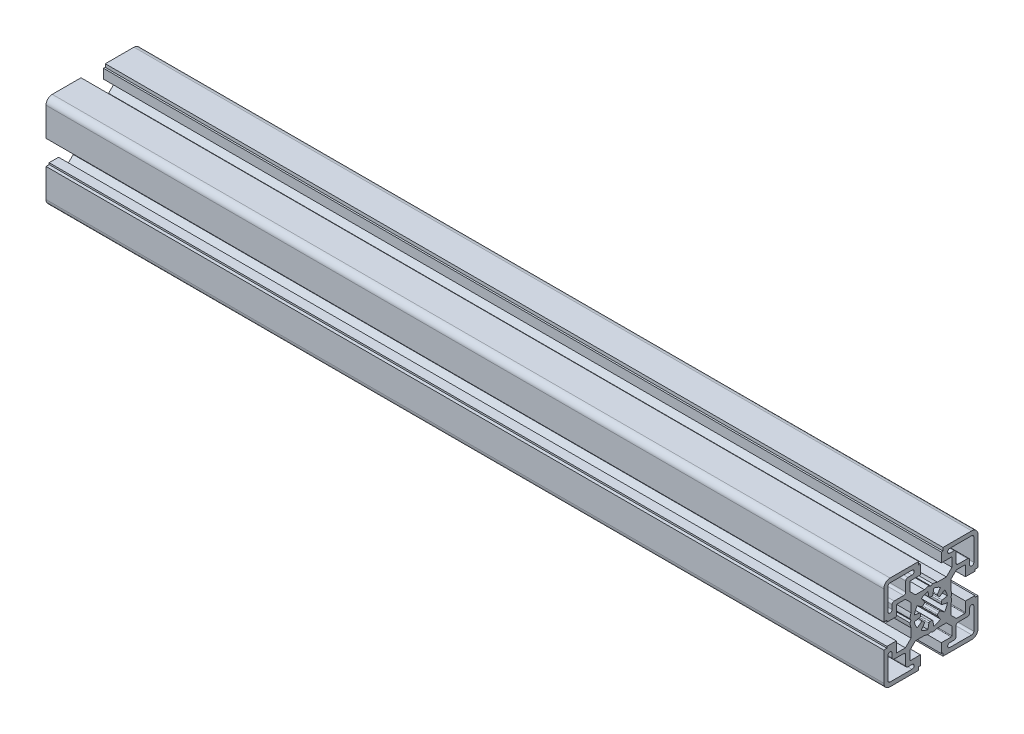
SolidWorks part; units mm, degrees
ref_plane "Спереди" through (0, 0, 0) normal (0, 0, 1) x (1, 0, 0)
ref_plane "Сверху" through (0, 0, 0) normal (0, 1, 0) x (1, 0, 0)
ref_plane "Справа" through (0, 0, 0) normal (1, 0, 0) x (0, 0, -1)
sketch "Эскиз2" plane through (0, 0, 0) normal (1, 0, 0) x (0, 0, -1)
  line L0 (-0.9511, 5.394) -> (-1.3892, 7.8785)
  line L1 (-3.1416, 4.4867) -> (-4.5886, 6.5532)
  line L2 (-4.4867, 3.1416) -> (-6.5532, 4.5886)
  line L3 (7.8785, -1.3892) -> (5.394, -0.9511)
  line L4 (-5.394, 0.9511) -> (-7.8785, 1.3892)
  line L5 (16.5, 5) -> (21, 5)
  line L6 (-21, 5) -> (-16.5, 5)
  line L7 (21, 5.8) -> (22.5, 5.8)
  line L8 (-22.5, 5.8) -> (-21, 5.8)
  line L9 (3.1225, 9.5) -> (7.3787, 9.5)
  line L10 (-7.3787, 9.5) -> (-3.1225, 9.5)
  line L11 (12.1713, 10.05) -> (16.2, 10.05)
  line L12 (-16.2, 10.05) -> (-12.1713, 10.05)
  line L13 (-17.5, 12) -> (-13, 12)
  line L14 (5, 16.5) -> (9.75, 16.5)
  line L15 (-9.75, 16.5) -> (-5, 16.5)
  line L16 (-19.5, 20.5) -> (-9, 20.5)
  line L17 (5, 21) -> (5.8, 21)
  line L18 (-5.8, 21) -> (-5, 21)
  line L19 (5.8, 22.5) -> (19.5, 22.5)
  line L20 (-19.5, 22.5) -> (-5.8, 22.5)
  line L21 (-7.8785, -1.3892) -> (-5.394, -0.9511)
  line L22 (5.394, 0.9511) -> (7.8785, 1.3892)
  line L23 (4.4867, 3.1416) -> (6.5532, 4.5886)
  line L24 (3.1416, 4.4867) -> (4.5886, 6.5532)
  line L25 (0.9511, 5.394) -> (1.3892, 7.8785)
  line L26 (-22.5, 5.8) -> (-22.5, 19.5)
  line L27 (-21, 5) -> (-21, 5.8)
  line L28 (-20.5, 9) -> (-20.5, 19.5)
  line L29 (-16.5, 5) -> (-16.5, 9.75)
  line L30 (-12, 13) -> (-12, 17.5)
  line L31 (-5.8, 21) -> (-5.8, 22.5)
  line L32 (-5, 16.5) -> (-5, 21)
  line L33 (5, 16.5) -> (5, 21)
  line L34 (5.8, 21) -> (5.8, 22.5)
  line L35 (9.5, 3.1225) -> (9.5, 7.3787)
  line L36 (10.05, 12.1713) -> (10.05, 16.2)
  line L37 (16.5, 5) -> (16.5, 9.75)
  line L38 (21, 5) -> (21, 5.8)
  line L39 (22.5, 5.8) -> (22.5, 19.5)
  line L40 (1.3892, -7.8785) -> (0.9511, -5.394)
  line L41 (4.5886, -6.5532) -> (3.1416, -4.4867)
  line L42 (6.5532, -4.5886) -> (4.4867, -3.1416)
  line L43 (-7.3787, -9.5) -> (-3.1225, -9.5)
  line L44 (3.1225, -9.5) -> (7.3787, -9.5)
  line L45 (-6.5532, -4.5886) -> (-4.4867, -3.1416)
  line L46 (-4.5886, -6.5532) -> (-3.1416, -4.4867)
  line L47 (-1.3892, -7.8785) -> (-0.9511, -5.394)
  line L48 (-9.5, -7.3787) -> (-9.5, -3.1225)
  line L49 (9.5, -7.3787) -> (9.5, -3.1225)
  line L50 (-22.5, -5.8) -> (-21, -5.8)
  line L51 (-21, -5) -> (-16.5, -5)
  line L52 (-21, -5.8) -> (-21, -5)
  line L53 (-16.5, -9.75) -> (-16.5, -5)
  line L54 (-22.5, -19.5) -> (-22.5, -5.8)
  line L55 (21, -5.8) -> (22.5, -5.8)
  line L56 (16.5, -5) -> (21, -5)
  line L57 (21, -5.8) -> (21, -5)
  line L58 (16.5, -9.75) -> (16.5, -5)
  line L59 (12.1713, -10.05) -> (16.2, -10.05)
  line L60 (22.5, -19.5) -> (22.5, -5.8)
  line L61 (-16.2, -10.05) -> (-12.1713, -10.05)
  line L62 (5, -16.5) -> (9.75, -16.5)
  line L63 (-9.75, -16.5) -> (-5, -16.5)
  line L64 (5, -21) -> (5.8, -21)
  line L65 (-5.8, -21) -> (-5, -21)
  line L66 (5.8, -22.5) -> (19.5, -22.5)
  line L67 (-19.5, -22.5) -> (-5.8, -22.5)
  line L68 (-10.05, -12.1713) -> (-10.05, -16.2)
  line L69 (-5.8, -21) -> (-5.8, -22.5)
  line L70 (-5, -16.5) -> (-5, -21)
  line L71 (5, -16.5) -> (5, -21)
  line L72 (5.8, -21) -> (5.8, -22.5)
  line L73 (10.05, -12.1713) -> (10.05, -16.2)
  line L74 (-9.5, 3.1225) -> (-9.5, 7.3787)
  line L75 (-9.5, 7.3787) -> (-12.1713, 10.05)
  line L76 (7.3787, 9.5) -> (10.05, 12.1713)
  line L77 (9.5, 7.3787) -> (12.1713, 10.05)
  line L78 (9.5, -7.3787) -> (12.1713, -10.05)
  line L79 (7.3787, -9.5) -> (10.05, -12.1713)
  line L80 (-7.3787, -9.5) -> (-10.05, -12.1713)
  line L81 (-12.1713, -10.05) -> (-9.5, -7.3787)
  line L82 (-10.05, 12.1713) -> (-10.05, 16.2)
  line L83 (-10.05, 12.1713) -> (-7.3787, 9.5)
  line L84 (-9.4624, 0) -> (-9.9624, 0.866)
  line L85 (-9.4624, 0) -> (-9.9624, -0.866)
  line L86 (0, -9.4624) -> (-0.866, -9.9624)
  line L87 (0, -9.4624) -> (0.866, -9.9624)
  line L88 (0, 9.4624) -> (0.866, 9.9624)
  line L89 (0, 9.4624) -> (-0.866, 9.9624)
  line L90 (9.4624, 0) -> (9.9624, -0.866)
  line L91 (9.4624, 0) -> (9.9624, 0.866)
  line L92 (-11, 18.5) -> (-9, 18.5)
  line L93 (-18.5, 11) -> (-18.5, 9)
  line L94 (17.5, 12) -> (13, 12)
  line L95 (12, 13) -> (12, 17.5)
  line L96 (19.5, 20.5) -> (9, 20.5)
  line L97 (11, 18.5) -> (9, 18.5)
  line L98 (20.5, 9) -> (20.5, 19.5)
  line L99 (18.5, 11) -> (18.5, 9)
  line L100 (-17.5, -12) -> (-13, -12)
  line L101 (-12, -13) -> (-12, -17.5)
  line L102 (-19.5, -20.5) -> (-9, -20.5)
  line L103 (-11, -18.5) -> (-9, -18.5)
  line L104 (-20.5, -9) -> (-20.5, -19.5)
  line L105 (-18.5, -11) -> (-18.5, -9)
  line L106 (19.5, -20.5) -> (9, -20.5)
  line L107 (11, -18.5) -> (9, -18.5)
  line L108 (17.5, -12) -> (13, -12)
  line L109 (12, -13) -> (12, -17.5)
  line L110 (20.5, -9) -> (20.5, -19.5)
  line L111 (18.5, -11) -> (18.5, -9)
  arc A0 (-19.5, 20.5) -> (-20.5, 19.5) centre (-19.5, 19.5) ccw
  arc A1 (-19.5, 22.5) -> (-22.5, 19.5) centre (-19.5, 19.5) ccw
  arc A2 (-13, 12) -> (-12, 13) centre (-13, 13) ccw
  arc A3 (-3.2283, 3.8181) -> (-3.8181, 3.2283) centre (0, 0) ccw
  arc A4 (3.8181, 3.2283) -> (3.2283, 3.8181) centre (0, 0) ccw
  arc A5 (-4.9826, 0.417) -> (-4.9826, -0.417) centre (0, 0) ccw
  arc A6 (0.417, 4.9826) -> (-0.417, 4.9826) centre (0, 0) ccw
  arc A7 (4.9826, -0.417) -> (4.9826, 0.417) centre (0, 0) ccw
  arc A8 (-6.5532, 4.5886) -> (-7.8785, 1.3892) centre (0, 0) ccw
  arc A9 (-1.3892, 7.8785) -> (-4.5886, 6.5532) centre (0, 0) ccw
  arc A10 (4.5886, 6.5532) -> (1.3892, 7.8785) centre (0, 0) ccw
  arc A11 (7.8785, 1.3892) -> (6.5532, 4.5886) centre (0, 0) ccw
  arc A12 (22.5, 19.5) -> (19.5, 22.5) centre (19.5, 19.5) ccw
  arc A13 (3.2283, -3.8181) -> (3.8181, -3.2283) centre (0, 0) ccw
  arc A14 (-3.8181, -3.2283) -> (-3.2283, -3.8181) centre (0, 0) ccw
  arc A15 (-0.417, -4.9826) -> (0.417, -4.9826) centre (0, 0) ccw
  arc A16 (6.5532, -4.5886) -> (7.8785, -1.3892) centre (0, 0) ccw
  arc A17 (1.3892, -7.8785) -> (4.5886, -6.5532) centre (0, 0) ccw
  arc A18 (-4.5886, -6.5532) -> (-1.3892, -7.8785) centre (0, 0) ccw
  arc A19 (-7.8785, -1.3892) -> (-6.5532, -4.5886) centre (0, 0) ccw
  arc A20 (-22.5, -19.5) -> (-19.5, -22.5) centre (-19.5, -19.5) ccw
  arc A21 (19.5, -22.5) -> (22.5, -19.5) centre (19.5, -19.5) ccw
  arc A22 (-4.4867, 3.1416) -> (-3.8181, 3.2283) centre (-4.1999, 3.5512) ccw
  arc A23 (-3.2283, 3.8181) -> (-3.1416, 4.4867) centre (-3.5512, 4.1999) ccw
  arc A24 (-0.9511, 5.394) -> (-0.417, 4.9826) centre (-0.4587, 5.4808) ccw
  arc A25 (0.417, 4.9826) -> (0.9511, 5.394) centre (0.4587, 5.4808) ccw
  arc A26 (3.1416, 4.4867) -> (3.2283, 3.8181) centre (3.5512, 4.1999) ccw
  arc A27 (3.8181, 3.2283) -> (4.4867, 3.1416) centre (4.1999, 3.5512) ccw
  arc A28 (5.394, 0.9511) -> (4.9826, 0.417) centre (5.4808, 0.4587) ccw
  arc A29 (4.9826, -0.417) -> (5.394, -0.9511) centre (5.4808, -0.4587) ccw
  arc A30 (4.4867, -3.1416) -> (3.8181, -3.2283) centre (4.1999, -3.5512) ccw
  arc A31 (3.2283, -3.8181) -> (3.1416, -4.4867) centre (3.5512, -4.1999) ccw
  arc A32 (0.9511, -5.394) -> (0.417, -4.9826) centre (0.4587, -5.4808) ccw
  arc A33 (-0.417, -4.9826) -> (-0.9511, -5.394) centre (-0.4587, -5.4808) ccw
  arc A34 (-3.1416, -4.4867) -> (-3.2283, -3.8181) centre (-3.5512, -4.1999) ccw
  arc A35 (-3.8181, -3.2283) -> (-4.4867, -3.1416) centre (-4.1999, -3.5512) ccw
  arc A36 (-5.394, -0.9511) -> (-4.9826, -0.417) centre (-5.4808, -0.4587) ccw
  arc A37 (-4.9826, 0.417) -> (-5.394, 0.9511) centre (-5.4808, 0.4587) ccw
  arc A38 (-16.5, -9.75) -> (-16.2, -10.05) centre (-16.2, -9.75) ccw
  arc A39 (-10.05, -16.2) -> (-9.75, -16.5) centre (-9.75, -16.2) ccw
  arc A40 (9.75, -16.5) -> (10.05, -16.2) centre (9.75, -16.2) ccw
  arc A41 (16.2, -10.05) -> (16.5, -9.75) centre (16.2, -9.75) ccw
  arc A42 (16.5, 9.75) -> (16.2, 10.05) centre (16.2, 9.75) ccw
  arc A43 (10.05, 16.2) -> (9.75, 16.5) centre (9.75, 16.2) ccw
  arc A44 (-9.75, 16.5) -> (-10.05, 16.2) centre (-9.75, 16.2) ccw
  arc A45 (-16.2, 10.05) -> (-16.5, 9.75) centre (-16.2, 9.75) ccw
  arc A46 (-9.9624, -0.866) -> (-9.5, -3.1225) centre (0, 0) ccw
  arc A47 (-9.5, 3.1225) -> (-9.9624, 0.866) centre (0, 0) ccw
  arc A48 (-3.1225, -9.5) -> (-0.866, -9.9624) centre (0, 0) ccw
  arc A49 (3.1225, 9.5) -> (0.866, 9.9624) centre (0, 0) ccw
  arc A50 (9.5, -3.1225) -> (9.9624, -0.866) centre (0, 0) ccw
  arc A51 (-0.866, 9.9624) -> (-3.1225, 9.5) centre (0, 0) ccw
  arc A52 (9.9624, 0.866) -> (9.5, 3.1225) centre (0, 0) ccw
  arc A53 (0.866, -9.9624) -> (3.1225, -9.5) centre (0, 0) ccw
  arc A54 (-11, 18.5) -> (-12, 17.5) centre (-11, 17.5) ccw
  arc A55 (-9, 18.5) -> (-9, 20.5) centre (-9, 19.5) ccw
  arc A56 (-17.5, 12) -> (-18.5, 11) centre (-17.5, 11) ccw
  arc A57 (-20.5, 9) -> (-18.5, 9) centre (-19.5, 9) ccw
  arc A58 (20.5, 19.5) -> (19.5, 20.5) centre (19.5, 19.5) ccw
  arc A59 (12, 13) -> (13, 12) centre (13, 13) ccw
  arc A60 (12, 17.5) -> (11, 18.5) centre (11, 17.5) ccw
  arc A61 (18.5, 11) -> (17.5, 12) centre (17.5, 11) ccw
  arc A62 (9, 20.5) -> (9, 18.5) centre (9, 19.5) ccw
  arc A63 (18.5, 9) -> (20.5, 9) centre (19.5, 9) ccw
  arc A64 (-20.5, -19.5) -> (-19.5, -20.5) centre (-19.5, -19.5) ccw
  arc A65 (-12, -13) -> (-13, -12) centre (-13, -13) ccw
  arc A66 (-12, -17.5) -> (-11, -18.5) centre (-11, -17.5) ccw
  arc A67 (-18.5, -11) -> (-17.5, -12) centre (-17.5, -11) ccw
  arc A68 (-9, -20.5) -> (-9, -18.5) centre (-9, -19.5) ccw
  arc A69 (-18.5, -9) -> (-20.5, -9) centre (-19.5, -9) ccw
  arc A70 (19.5, -20.5) -> (20.5, -19.5) centre (19.5, -19.5) ccw
  arc A71 (11, -18.5) -> (12, -17.5) centre (11, -17.5) ccw
  arc A72 (9, -18.5) -> (9, -20.5) centre (9, -19.5) ccw
  arc A73 (13, -12) -> (12, -13) centre (13, -13) ccw
  arc A74 (17.5, -12) -> (18.5, -11) centre (17.5, -11) ccw
  arc A75 (20.5, -9) -> (18.5, -9) centre (19.5, -9) ccw
extrude "Бобышка-Вытянуть1" add sketch "Эскиз2" along normal blind 400 contours L75 L12 A45 L29 L6 L27 L8 L26 A1 L20 L31 L18 L32 L15 A44 L82 L83 L10 A51 L89 L88 A49 L9 L76 L36 A43 L14 L33 L17 L34 L19 A12 L39 L7 L38 L5 L37 A42 L11 L77 L35 A52 L91 L90 A50 L49 L78 L59 A41 L58 L56 L57 L55 L60 A21 L66 L72 L64 L71 L62 A40 L73 L79 L44 A53 L87 L86 A48 L43 L80 L68 A39 L63 L70 L65 L69 L67 A20 L54 L50 L52 L51 L53 A38 L61 L81 L48 A46 L85 L84 A47 L74
sketch "Эскиз3" plane through (0, 0, 0) normal (-1, 0, 0) x (0, 0, 1)
  line L0 (-0.9511, 5.394) -> (-1.3892, 7.8785)
  line L1 (-3.1416, 4.4867) -> (-4.5886, 6.5532)
  line L2 (-4.4867, 3.1416) -> (-6.5532, 4.5886)
  line L3 (7.8785, -1.3892) -> (5.394, -0.9511)
  line L4 (-5.394, 0.9511) -> (-7.8785, 1.3892)
  line L13 (-17.5, 12) -> (-13, 12)
  line L16 (-19.5, 20.5) -> (-9, 20.5)
  line L21 (-7.8785, -1.3892) -> (-5.394, -0.9511)
  line L22 (5.394, 0.9511) -> (7.8785, 1.3892)
  line L23 (4.4867, 3.1416) -> (6.5532, 4.5886)
  line L24 (3.1416, 4.4867) -> (4.5886, 6.5532)
  line L25 (0.9511, 5.394) -> (1.3892, 7.8785)
  line L28 (-20.5, 9) -> (-20.5, 19.5)
  line L30 (-12, 13) -> (-12, 17.5)
  line L40 (1.3892, -7.8785) -> (0.9511, -5.394)
  line L41 (4.5886, -6.5532) -> (3.1416, -4.4867)
  line L42 (6.5532, -4.5886) -> (4.4867, -3.1416)
  line L45 (-6.5532, -4.5886) -> (-4.4867, -3.1416)
  line L46 (-4.5886, -6.5532) -> (-3.1416, -4.4867)
  line L47 (-1.3892, -7.8785) -> (-0.9511, -5.394)
  line L92 (-11, 18.5) -> (-9, 18.5)
  line L93 (-18.5, 11) -> (-18.5, 9)
  line L94 (17.5, 12) -> (13, 12)
  line L95 (12, 13) -> (12, 17.5)
  line L96 (19.5, 20.5) -> (9, 20.5)
  line L97 (11, 18.5) -> (9, 18.5)
  line L98 (20.5, 9) -> (20.5, 19.5)
  line L99 (18.5, 11) -> (18.5, 9)
  line L100 (-17.5, -12) -> (-13, -12)
  line L101 (-12, -13) -> (-12, -17.5)
  line L102 (-19.5, -20.5) -> (-9, -20.5)
  line L103 (-11, -18.5) -> (-9, -18.5)
  line L104 (-20.5, -9) -> (-20.5, -19.5)
  line L105 (-18.5, -11) -> (-18.5, -9)
  line L106 (19.5, -20.5) -> (9, -20.5)
  line L107 (11, -18.5) -> (9, -18.5)
  line L108 (17.5, -12) -> (13, -12)
  line L109 (12, -13) -> (12, -17.5)
  line L110 (20.5, -9) -> (20.5, -19.5)
  line L111 (18.5, -11) -> (18.5, -9)
  arc A0 (-19.5, 20.5) -> (-20.5, 19.5) centre (-19.5, 19.5) ccw
  arc A2 (-13, 12) -> (-12, 13) centre (-13, 13) ccw
  arc A3 (-3.2283, 3.8181) -> (-3.8181, 3.2283) centre (0, 0) ccw
  arc A4 (3.8181, 3.2283) -> (3.2283, 3.8181) centre (0, 0) ccw
  arc A5 (-4.9826, 0.417) -> (-4.9826, -0.417) centre (0, 0) ccw
  arc A6 (0.417, 4.9826) -> (-0.417, 4.9826) centre (0, 0) ccw
  arc A7 (4.9826, -0.417) -> (4.9826, 0.417) centre (0, 0) ccw
  arc A8 (-6.5532, 4.5886) -> (-7.8785, 1.3892) centre (0, 0) ccw
  arc A9 (-1.3892, 7.8785) -> (-4.5886, 6.5532) centre (0, 0) ccw
  arc A10 (4.5886, 6.5532) -> (1.3892, 7.8785) centre (0, 0) ccw
  arc A11 (7.8785, 1.3892) -> (6.5532, 4.5886) centre (0, 0) ccw
  arc A13 (3.2283, -3.8181) -> (3.8181, -3.2283) centre (0, 0) ccw
  arc A14 (-3.8181, -3.2283) -> (-3.2283, -3.8181) centre (0, 0) ccw
  arc A15 (-0.417, -4.9826) -> (0.417, -4.9826) centre (0, 0) ccw
  arc A16 (6.5532, -4.5886) -> (7.8785, -1.3892) centre (0, 0) ccw
  arc A17 (1.3892, -7.8785) -> (4.5886, -6.5532) centre (0, 0) ccw
  arc A18 (-4.5886, -6.5532) -> (-1.3892, -7.8785) centre (0, 0) ccw
  arc A19 (-7.8785, -1.3892) -> (-6.5532, -4.5886) centre (0, 0) ccw
  arc A22 (-4.4867, 3.1416) -> (-3.8181, 3.2283) centre (-4.1999, 3.5512) ccw
  arc A23 (-3.2283, 3.8181) -> (-3.1416, 4.4867) centre (-3.5512, 4.1999) ccw
  arc A24 (-0.9511, 5.394) -> (-0.417, 4.9826) centre (-0.4587, 5.4808) ccw
  arc A25 (0.417, 4.9826) -> (0.9511, 5.394) centre (0.4587, 5.4808) ccw
  arc A26 (3.1416, 4.4867) -> (3.2283, 3.8181) centre (3.5512, 4.1999) ccw
  arc A27 (3.8181, 3.2283) -> (4.4867, 3.1416) centre (4.1999, 3.5512) ccw
  arc A28 (5.394, 0.9511) -> (4.9826, 0.417) centre (5.4808, 0.4587) ccw
  arc A29 (4.9826, -0.417) -> (5.394, -0.9511) centre (5.4808, -0.4587) ccw
  arc A30 (4.4867, -3.1416) -> (3.8181, -3.2283) centre (4.1999, -3.5512) ccw
  arc A31 (3.2283, -3.8181) -> (3.1416, -4.4867) centre (3.5512, -4.1999) ccw
  arc A32 (0.9511, -5.394) -> (0.417, -4.9826) centre (0.4587, -5.4808) ccw
  arc A33 (-0.417, -4.9826) -> (-0.9511, -5.394) centre (-0.4587, -5.4808) ccw
  arc A34 (-3.1416, -4.4867) -> (-3.2283, -3.8181) centre (-3.5512, -4.1999) ccw
  arc A35 (-3.8181, -3.2283) -> (-4.4867, -3.1416) centre (-4.1999, -3.5512) ccw
  arc A36 (-5.394, -0.9511) -> (-4.9826, -0.417) centre (-5.4808, -0.4587) ccw
  arc A37 (-4.9826, 0.417) -> (-5.394, 0.9511) centre (-5.4808, 0.4587) ccw
  arc A54 (-11, 18.5) -> (-12, 17.5) centre (-11, 17.5) ccw
  arc A55 (-9, 18.5) -> (-9, 20.5) centre (-9, 19.5) ccw
  arc A56 (-17.5, 12) -> (-18.5, 11) centre (-17.5, 11) ccw
  arc A57 (-20.5, 9) -> (-18.5, 9) centre (-19.5, 9) ccw
  arc A58 (20.5, 19.5) -> (19.5, 20.5) centre (19.5, 19.5) ccw
  arc A59 (12, 13) -> (13, 12) centre (13, 13) ccw
  arc A60 (12, 17.5) -> (11, 18.5) centre (11, 17.5) ccw
  arc A61 (18.5, 11) -> (17.5, 12) centre (17.5, 11) ccw
  arc A62 (9, 20.5) -> (9, 18.5) centre (9, 19.5) ccw
  arc A63 (18.5, 9) -> (20.5, 9) centre (19.5, 9) ccw
  arc A64 (-20.5, -19.5) -> (-19.5, -20.5) centre (-19.5, -19.5) ccw
  arc A65 (-12, -13) -> (-13, -12) centre (-13, -13) ccw
  arc A66 (-12, -17.5) -> (-11, -18.5) centre (-11, -17.5) ccw
  arc A67 (-18.5, -11) -> (-17.5, -12) centre (-17.5, -11) ccw
  arc A68 (-9, -20.5) -> (-9, -18.5) centre (-9, -19.5) ccw
  arc A69 (-18.5, -9) -> (-20.5, -9) centre (-19.5, -9) ccw
  arc A70 (19.5, -20.5) -> (20.5, -19.5) centre (19.5, -19.5) ccw
  arc A71 (11, -18.5) -> (12, -17.5) centre (11, -17.5) ccw
  arc A72 (9, -18.5) -> (9, -20.5) centre (9, -19.5) ccw
  arc A73 (13, -12) -> (12, -13) centre (13, -13) ccw
  arc A74 (17.5, -12) -> (18.5, -11) centre (17.5, -11) ccw
  arc A75 (20.5, -9) -> (18.5, -9) centre (19.5, -9) ccw
extrude "Вырез-Вытянуть1" cut sketch "Эскиз3" against normal through all
